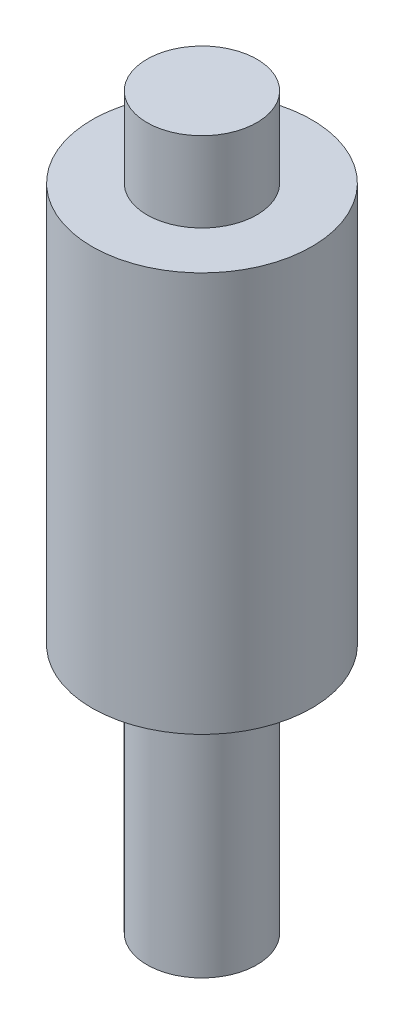
SolidWorks part; units mm, degrees
ref_plane "Front Plane" through (0, 0, 0) normal (0, 0, 1) x (1, 0, 0)
ref_plane "Top Plane" through (0, 0, 0) normal (0, 1, 0) x (1, 0, 0)
ref_plane "Right Plane" through (0, 0, 0) normal (1, 0, 0) x (0, 0, -1)
sketch "Sketch1" plane through (0, 0, 0) normal (0, 1, 0) x (1, 0, 0)
  circle A0 centre (0, 0) radius 2.2
  dimension "D1" = 4.4
extrude "Boss-Extrude1" add sketch "Sketch1" along normal blind 8
sketch "Sketch2" plane through (0, 8, 0) normal (0, 1, 0) x (1, 0, 0)
  circle A0 centre (0, 0) radius 1.1
  dimension "D1" = 2.2
extrude "Boss-Extrude2" add sketch "Sketch2" along normal blind 1.6
sketch "Sketch3" plane through (0, 0, 0) normal (0, -1, 0) x (1, 0, 0)
  circle A0 centre (0, 0) radius 1.1
  dimension "D1" = 2.2
extrude "Boss-Extrude3" add sketch "Sketch3" along normal blind 5
